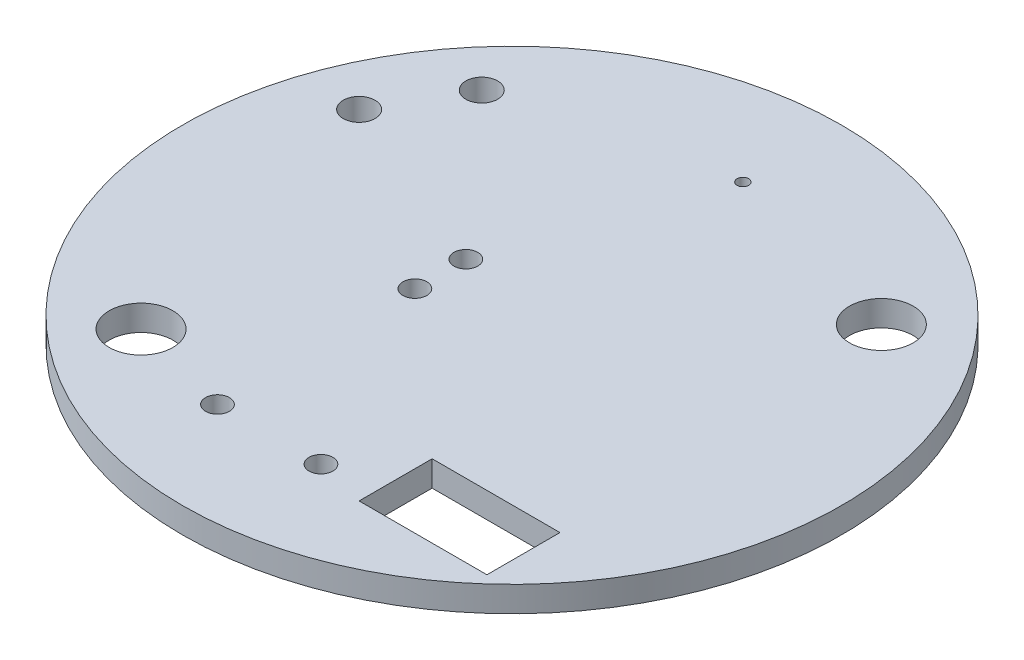
SolidWorks part; units mm, degrees
material "Плата системы питания"
ref_plane "Спереди" through (0, 0, 0) normal (0, 0, 1) x (1, 0, 0)
ref_plane "Сверху" through (0, 0, 0) normal (0, 1, 0) x (1, 0, 0)
ref_plane "Справа" through (0, 0, 0) normal (1, 0, 0) x (0, 0, -1)
sketch "Эскиз1" plane through (0, 0, 0) normal (0, 1, 0) x (1, 0, 0)
  line L0 (5.2956, -14.9005) -> (13.3259, -14.9005)
  line L1 (5.2956, -14.9005) -> (5.2956, -10.3118)
  line L2 (13.3259, -14.9005) -> (13.3259, -10.3118)
  line L3 (5.2956, -10.3118) -> (13.3259, -10.3118)
  line L4 (5.2956, -14.9005) -> (13.3259, -10.3118) construction
  line L5 (13.3259, -14.9005) -> (5.2956, -10.3118) construction
  circle A0 centre (0, 0) radius 20.7
  circle A1 centre (12.1, 11.1) radius 2
  circle A2 centre (-10.9, -12.4) radius 2
  circle A3 centre (-16, 6.4) radius 1
  circle A4 centre (-13.2, 11.3) radius 1
  circle A5 centre (0, 14.5) radius 0.3639
  circle A6 centre (-4.5, 1.6) radius 0.75
  circle A7 centre (-4.5, -1.6) radius 0.75
  circle A8 centre (-4.4, -14.1) radius 0.75
  circle A9 centre (2.1, -14.1) radius 0.75
  point P22 (9.3107, -12.6061)
extrude "Бобышка-Вытянуть1" add sketch "Эскиз1" along normal blind 1.6
